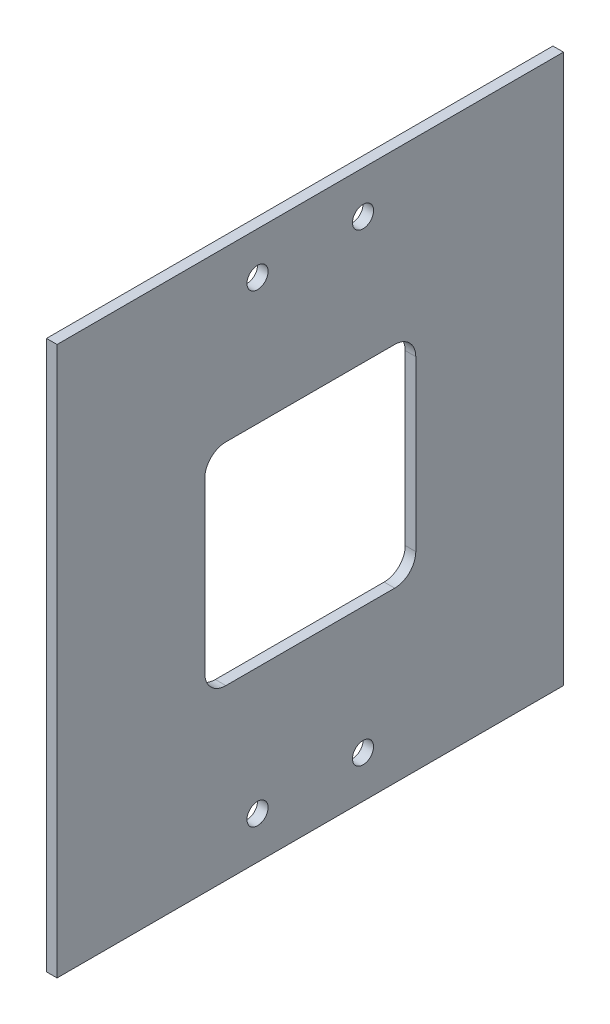
SolidWorks part; units mm, degrees
material "ASTM A36 Steel"
ref_plane "Front Plane" through (0, 0, 0) normal (0, 0, 1) x (1, 0, 0)
ref_plane "Top Plane" through (0, 0, 0) normal (0, 1, 0) x (1, 0, 0)
ref_plane "Right Plane" through (0, 0, 0) normal (1, 0, 0) x (0, 0, -1)
sketch "Sketch1" plane through (0, 0, 0) normal (1, 0, 0) x (0, 0, -1)
  line L0 (0, 2.6194) -> (0, -2.6194) construction
  line L1 (152.4, 82.55) -> (0, 82.55)
  line L2 (152.4, 82.55) -> (152.4, -82.55)
  line L3 (152.4, -82.55) -> (0, -82.55)
  line L4 (0, 82.55) -> (0, -82.55)
  line L5 (152.4, 82.55) -> (0, -82.55) construction
  line L6 (152.4, -82.55) -> (0, 82.55) construction
  line L7 (2.6194, 0) -> (-2.6194, 0) construction
  point P0 (76.2, 0)
  dimension "D1" = 152.4
  dimension "D2" = 165.1
extrude "Boss-Extrude1" add sketch "Sketch1" along normal blind 3.175
sketch "Sketch2" plane through (0, 0, 0) normal (-1, 0, 0) x (0, 0, 1)
  line L0 (-107.95, 25.4) -> (-107.95, -25.4)
  line L1 (-101.6, -31.75) -> (-50.8, -31.75)
  line L2 (-44.45, -25.4) -> (-44.45, 25.4)
  line L3 (-50.8, 31.75) -> (-101.6, 31.75)
  line L4 (-76.2, 31.75) -> (-76.2, -31.75) construction
  line L5 (0, 0) -> (-152.4, 0)
  line L6 (-152.4, -82.55) -> (-152.4, 82.55) construction
  arc A0 (-107.95, -25.4) -> (-101.6, -31.75) centre (-101.6, -25.4) ccw
  arc A1 (-50.8, -31.75) -> (-44.45, -25.4) centre (-50.8, -25.4) ccw
  arc A2 (-44.45, 25.4) -> (-50.8, 31.75) centre (-50.8, 25.4) ccw
  arc A3 (-101.6, 31.75) -> (-107.95, 25.4) centre (-101.6, 25.4) ccw
  point P19 (-76.2, 0)
  dimension "D1" = 6.35
  dimension "D2" = 63.5
  dimension "D3" = 63.5
extrude "Cut-Extrude1" cut sketch "Sketch2" against normal through all contours L4 L5 L0 A0 L1 | L4 L3 A3 L0 L5 | L3 L4 L5 L2 A2 | L5 L4 L1 A1 L2
sketch "Sketch3" plane through (0, 0, 0) normal (-1, 0, 0) x (0, 0, 1)
  line L0 (-76.2, 82.55) -> (-76.2, -82.55) construction
  line L1 (-152.4, 82.55) -> (0, 82.55) construction
  line L2 (0, -82.55) -> (-152.4, -82.55) construction
  line L3 (-92.075, -69.85) -> (-60.325, -69.85) construction
  line L4 (-92.075, 69.85) -> (-60.325, 69.85) construction
  circle A0 centre (-60.325, 69.85) radius 3.175
  circle A1 centre (-92.075, 69.85) radius 3.175
  circle A2 centre (-92.075, -69.85) radius 3.175
  circle A3 centre (-60.325, -69.85) radius 3.175
  point P10 (-76.2, 69.85)
  point P11 (-76.2, -69.85)
  dimension "D1" = 6.35
  dimension "D2" = 12.7
  dimension "D3" = 31.75
  dimension "D4" = 12.7
extrude "Cut-Extrude2" cut sketch "Sketch3" against normal through all
sketch3d "TAG"
  line L0 (0, 82.55, -152.4) -> (0, 82.55, 0) construction
  line L1 (3.175, 82.55, 0) -> (0, 82.55, 0) construction
  line L2 (0, 82.55, 0) -> (0, -82.55, 0) construction
  line L3 (0, 82.55, -152.4) -> (0, 82.55, 0)
  line L4 (3.175, 82.55, 0) -> (0, 82.55, 0)
  line L5 (0, 82.55, 0) -> (0, -82.55, 0)
  dimension "D1" = 3.175
  dimension "D2" = 152.4
  dimension "D3" = 165.1
